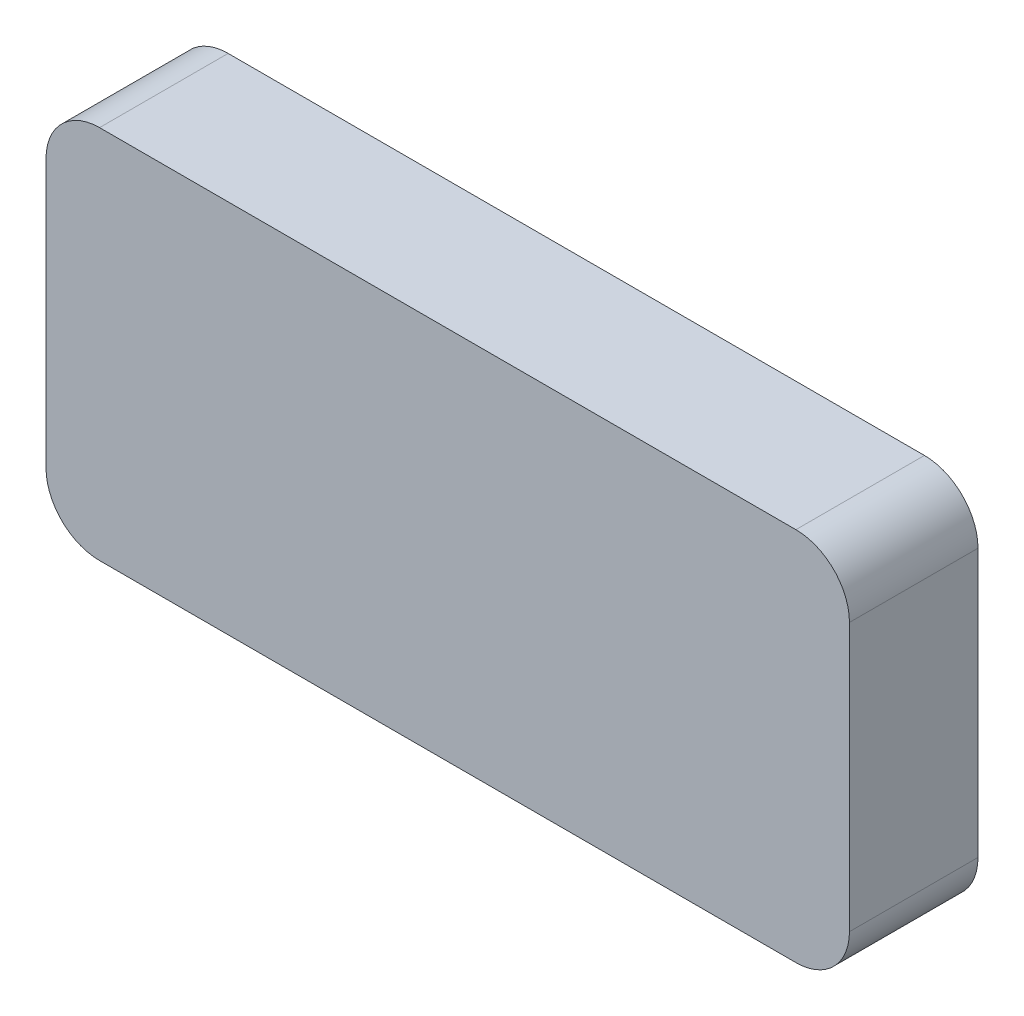
SolidWorks part; units mm, degrees
ref_plane "Front Plane" through (0, 0, 0) normal (0, 0, 1) x (1, 0, 0)
ref_plane "Top Plane" through (0, 0, 0) normal (0, 1, 0) x (1, 0, 0)
ref_plane "Right Plane" through (0, 0, 0) normal (1, 0, 0) x (0, 0, -1)
sketch "Sketch1" plane through (0, 0, 0) normal (0, 0, 1) x (1, 0, 0)
  line L1 (0, 0) -> (75, 0)
  line L2 (0, 0) -> (0, 35)
  line L3 (0, 35) -> (75, 35)
  line L4 (75, 0) -> (75, 35)
  dimension "D1" = 75
  dimension "D2" = 35
extrude "Boss-Extrude1" add sketch "Sketch1" along normal blind 12
fillet "Fillet1" radius 5 4 edges at (0, 0, 6) (75, 0, 6) (75, 35, 6) (0, 35, 6)
